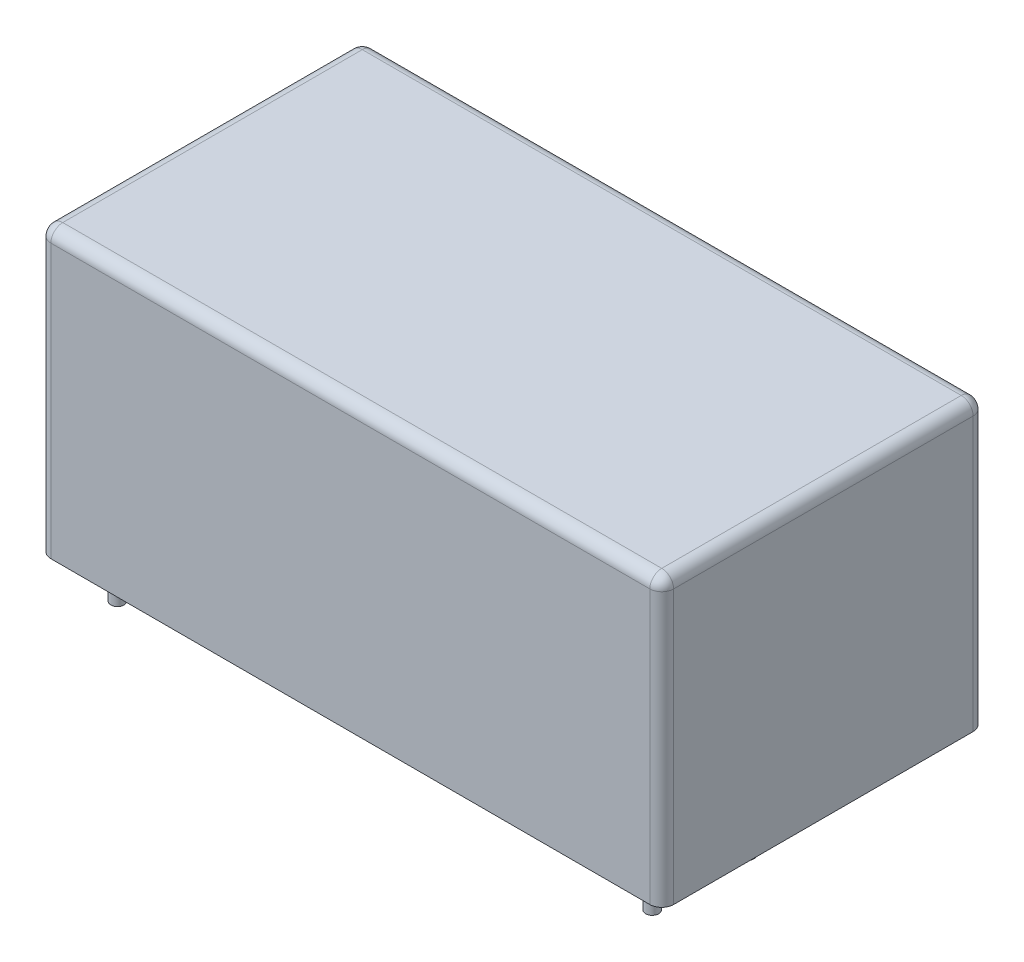
SolidWorks part; units mm, degrees
ref_plane "Спереди" through (0, 0, 0) normal (0, 0, 1) x (1, 0, 0)
ref_plane "Сверху" through (0, 0, 0) normal (0, 1, 0) x (1, 0, 0)
ref_plane "Справа" through (0, 0, 0) normal (1, 0, 0) x (0, 0, -1)
sketch "Эскиз1" plane through (0, 0, 0) normal (0, 1, 0) x (1, 0, 0)
  line L1 (-25.2, 13.6) -> (25.2, 13.6)
  line L2 (-26.2, 12.6) -> (-26.2, -12.6)
  line L3 (-25.2, -13.6) -> (25.2, -13.6)
  line L4 (26.2, 12.6) -> (26.2, -12.6)
  line L5 (-26.2, 13.6) -> (26.2, -13.6) construction
  line L6 (-26.2, -13.6) -> (26.2, 13.6) construction
  arc A0 (25.2, 13.6) -> (26.2, 12.6) centre (25.2, 12.6) cw
  arc A1 (26.2, -12.6) -> (25.2, -13.6) centre (25.2, -12.6) cw
  arc A2 (-25.2, -13.6) -> (-26.2, -12.6) centre (-25.2, -12.6) cw
  arc A3 (-26.2, 12.6) -> (-25.2, 13.6) centre (-25.2, 12.6) cw
  point P0 (0, 0)
  dimension "D3" = 1
  dimension "D1" = 52.4
  dimension "D2" = 27.2
extrude "Бобышка-Вытянуть1" add sketch "Эскиз1" along normal blind 24
fillet "Скругление1" radius 1 8 edges at (-25.9071, 24, 13.3071) (-25.9071, 24, -13.3071) (25.9071, 24, -13.3071) (25.9071, 24, 13.3071) (-26.2, 24, 0) (0, 24, -13.6) (26.2, 24, 0) (0, 24, 13.6)
sketch "Ноги" plane through (0, 0, 0) normal (0, -1, 0) x (1, 0, 0)
  line L0 (-26.2, -12.6) -> (-26.2, 12.6) construction
  line L1 (-25.2, 13.6) -> (25.2, 13.6) construction
  circle A0 centre (-22.8, 10.4) radius 0.55
  circle A1 centre (-22.8, -10.4) radius 0.55
  circle A2 centre (22.2, 10.4) radius 0.55
  circle A3 centre (22.2, 2.4) radius 0.55
  dimension "D1" = 1.1
  dimension "D4" = 1.1
  dimension "D6" = 20.8
  dimension "D7" = 1.1
  dimension "D8" = 1.1
  dimension "D12" = 45
  dimension "D2" = 3.4
  dimension "D3" = 3.2
  dimension "D5" = 3.4
  dimension "D9" = 45
  dimension "D10" = 3.2
  dimension "D11" = 8
extrude "Бобышка-Вытянуть2" add sketch "Ноги" along normal blind 3.5
